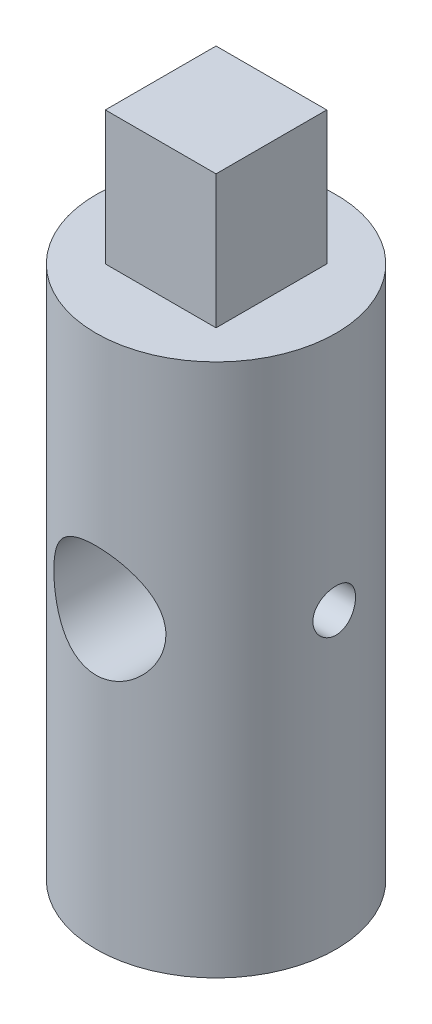
SolidWorks part; units mm, degrees
ref_plane "前视基准面" through (0, 0, 0) normal (0, 0, 1) x (1, 0, 0)
ref_plane "上视基准面" through (0, 0, 0) normal (0, 1, 0) x (1, 0, 0)
ref_plane "右视基准面" through (0, 0, 0) normal (1, 0, 0) x (0, 0, -1)
sketch "草图1" plane through (0, 0, 0) normal (0, 1, 0) x (1, 0, 0)
  circle A0 centre (0, 0) radius 9
  dimension "D1" = 18
extrude "凸台-拉伸1" add sketch "草图1" along normal blind 40
sketch "草图2" plane through (0, 0, 0) normal (0, -1, 0) x (1, 0, 0)
  circle A0 centre (0, 0) radius 3.2
  dimension "D1" = 6.4
extrude "切除-拉伸1" cut sketch "草图2" against normal blind 17
sketch "草图15" plane through (0, 40, 0) normal (0, 1, 0) x (1, 0, 0)
  line L1 (-4.15, -4.15) -> (4.15, -4.15)
  line L2 (-4.15, -4.15) -> (-4.15, 4.15)
  line L3 (-4.15, 4.15) -> (4.15, 4.15)
  line L4 (4.15, -4.15) -> (4.15, 4.15)
  dimension "D1" = 8.3
  dimension "D2" = 8.3
  dimension "D3" = 4.15
  dimension "D4" = 4.15
extrude "凸台-拉伸2" add sketch "草图15" along normal blind 10
sketch "草图16" plane through (0, 0, 0) normal (0, 0, 1) x (1, 0, 0)
  line L0 (-9, 0) -> (9, 0) construction
  circle A0 centre (0, 22) radius 4.2
  dimension "D2" = 8.4
  dimension "D1" = 22
extrude "切除-拉伸2" cut sketch "草图16" against normal mid plane 20
sketch "草图17" plane through (0, 0, 0) normal (1, 0, 0) x (0, 0, -1)
  line L0 (-9, 0) -> (9, 0) construction
  circle A0 centre (0, 22) radius 1.6
  dimension "D2" = 3.2
  dimension "D1" = 22
extrude "切除-拉伸3" cut sketch "草图17" against normal mid plane 20
